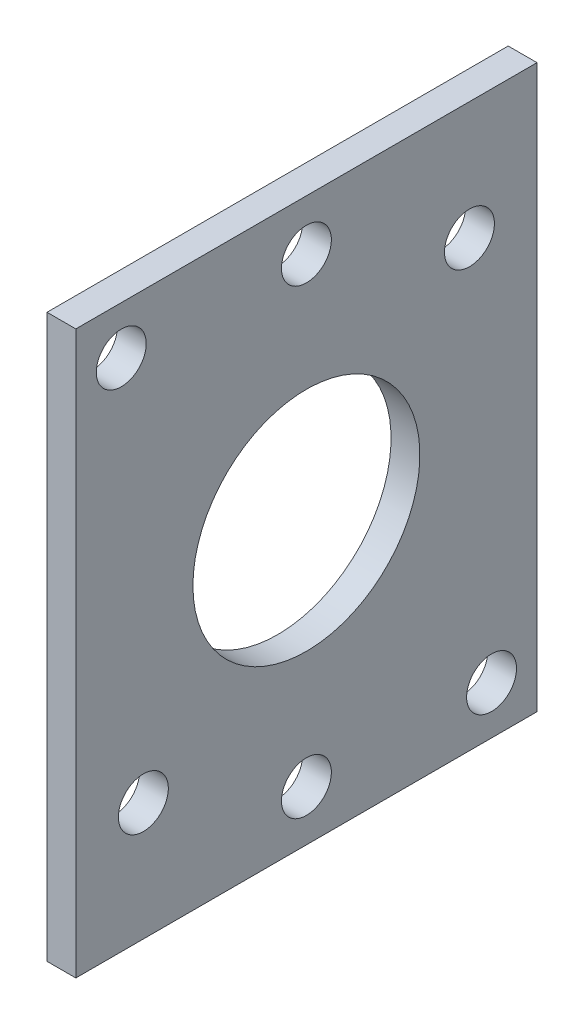
SolidWorks part; units mm, degrees
ref_plane "Front Plane" through (0, 0, 0) normal (0, 0, 1) x (1, 0, 0)
ref_plane "Top Plane" through (0, 0, 0) normal (0, 1, 0) x (1, 0, 0)
ref_plane "Right Plane" through (0, 0, 0) normal (1, 0, 0) x (0, 0, -1)
sketch "Sketch1" plane through (0, 0, 0) normal (1, 0, 0) x (0, 0, -1)
  line L45 (0, 0) -> (50.8, 0)
  line L46 (0, 0) -> (0, 61.92)
  line L47 (0, 61.92) -> (50.8, 61.92)
  line L48 (50.8, 0) -> (50.8, 61.92)
  dimension "D1" = 61.92
  dimension "D2" = 50.8
extrude "Boss-Extrude2" add sketch "Sketch1" along normal blind 3.175
sketch "Sketch2" plane through (0, 0, 0) normal (-1, 0, 0) x (0, 0, 1)
  line L0 (-50.8, 0) -> (-50.8, 61.92) construction
  line L3 (0, 0) -> (-50.8, 0) construction
  line L4 (0, 61.92) -> (0, 0) construction
  circle A3 centre (-25.3997, 56.36) radius 2.75
  circle A4 centre (-25.3997, 30.96) radius 25.4 construction
  circle A6 centre (-43.3599, 48.9208) radius 2.75
  circle A8 centre (-5.0045, 56.6481) radius 2.75
  circle A9 centre (-7.4395, 13.0002) radius 2.75
  circle A10 centre (-45.7955, 5.2725) radius 2.75
  circle A11 centre (-25.3997, 5.5607) radius 2.75
  circle A13 centre (-25.3997, 30.96) radius 12.5
  point P3 (0, 0)
  point P5 (0, 0)
  point P13 (0, 0)
  point P22 (0, 0)
  point P23 (0, 0)
  point P24 (0, 0)
  point P27 (-50.8, 30.96)
  dimension "D1" = 25
  dimension "D13" = 5.5
  dimension "D16" = 5.5
  dimension "D17" = 5.5
  dimension "D18" = 5.5
  dimension "D3" = 50.8
  dimension "D4" = 5.5
  dimension "D5" = 5.5
  dimension "D10" = 32.8
  dimension "D6" = 19.44
  dimension "D7" = 19.44
  dimension "D8" = 32.8
  dimension "D9" = 5.5607
  dimension "D11" = 7.4395
  dimension "D20" = 7.4395
extrude "Cut-Extrude1" cut sketch "Sketch2" against normal through all
